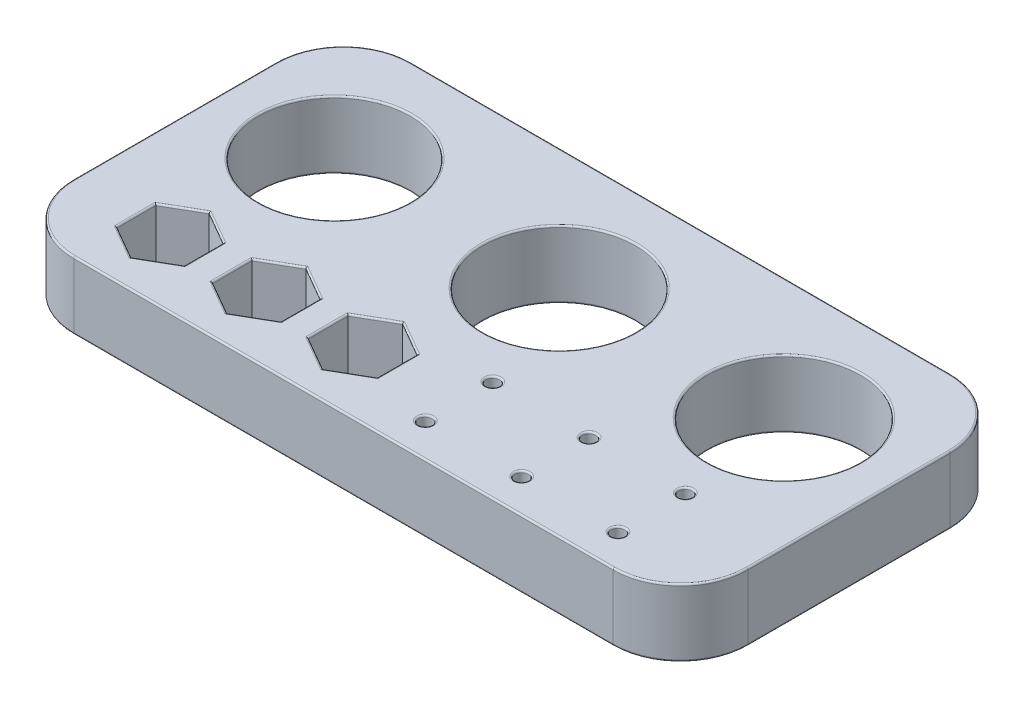
SolidWorks part; units mm, degrees
ref_plane "Front Plane" through (0, 0, 0) normal (0, 0, 1) x (1, 0, 0)
ref_plane "Top Plane" through (0, 0, 0) normal (0, 1, 0) x (1, 0, 0)
ref_plane "Right Plane" through (0, 0, 0) normal (1, 0, 0) x (0, 0, -1)
sketch "Sketch1" plane through (0, 0, 0) normal (0, 1, 0) x (1, 0, 0)
  line L0 (-63.5, -19.05) -> (-45.3571, -19.05) construction
  line L1 (-63.5, -31.75) -> (63.5, -31.75)
  line L2 (-63.5, -31.75) -> (-63.5, 31.75)
  line L3 (-63.5, 31.75) -> (63.5, 31.75)
  line L4 (63.5, -31.75) -> (63.5, 31.75)
  line L5 (-63.5, -31.75) -> (63.5, 31.75) construction
  line L6 (-63.5, 31.75) -> (63.5, -31.75) construction
  line L7 (-39.0071, -15.3838) -> (-45.3571, -11.7177)
  line L8 (-45.3571, -11.7177) -> (-51.7071, -15.3838)
  line L9 (-51.7071, -15.3838) -> (-51.7071, -22.7162)
  line L10 (-51.7071, -22.7162) -> (-45.3571, -26.3823)
  line L11 (-45.3571, -26.3823) -> (-39.0071, -22.7162)
  line L12 (-39.0071, -22.7162) -> (-39.0071, -15.3838)
  line L13 (-45.3571, -19.05) -> (-27.2143, -19.05) construction
  line L14 (-27.2143, -19.05) -> (-9.0714, -19.05) construction
  line L15 (-9.0714, -19.05) -> (9.0714, -19.05) construction
  line L16 (9.0714, -19.05) -> (27.2143, -19.05) construction
  line L17 (27.2143, -19.05) -> (45.3571, -19.05) construction
  line L18 (63.5, 8.89) -> (42.3333, 8.89) construction
  line L19 (42.3333, 8.89) -> (21.1667, 8.89) construction
  line L20 (21.1667, 8.89) -> (0, 8.89) construction
  line L21 (0, 8.89) -> (-21.1667, 8.89) construction
  line L22 (-21.1667, 8.89) -> (-42.3333, 8.89) construction
  line L23 (-42.3333, 8.89) -> (-63.5, 8.89) construction
  line L24 (-63.5, -29.21) -> (-42.3333, -29.21) construction
  line L25 (-20.7893, -22.7595) -> (-20.7893, -15.3405)
  line L26 (-20.7893, -15.3405) -> (-27.2143, -11.631)
  line L27 (-27.2143, -11.631) -> (-33.6393, -15.3405)
  line L28 (-33.6393, -15.3405) -> (-33.6393, -22.7595)
  line L29 (-33.6393, -22.7595) -> (-27.2143, -26.469)
  line L30 (-27.2143, -26.469) -> (-20.7893, -22.7595)
  line L31 (-2.5714, -22.8028) -> (-2.5714, -15.2972)
  line L32 (-2.5714, -15.2972) -> (-9.0714, -11.5444)
  line L33 (-9.0714, -11.5444) -> (-15.5714, -15.2972)
  line L34 (-15.5714, -15.2972) -> (-15.5714, -22.8028)
  line L35 (-15.5714, -22.8028) -> (-9.0714, -26.5556)
  line L36 (-9.0714, -26.5556) -> (-2.5714, -22.8028)
  line L49 (-42.3333, -29.21) -> (-21.1667, -29.21) construction
  line L50 (-21.1667, -29.21) -> (0, -29.21) construction
  line L51 (0, -29.21) -> (21.1667, -29.21) construction
  line L52 (21.1667, -29.21) -> (42.3333, -29.21) construction
  line L53 (42.3333, -29.21) -> (63.5, -29.21) construction
  line L58 (45.3571, -19.05) -> (63.5, -19.05) construction
  line L71 (0, -12.7) -> (9.0714, -12.7) construction
  line L79 (9.0714, -12.7) -> (27.2143, -12.7) construction
  line L80 (0, -19.05) -> (0, -12.7) construction
  line L81 (0, -19.05) -> (0, -25.4) construction
  line L82 (27.2143, -12.7) -> (45.3571, -12.7) construction
  line L83 (45.3571, -12.7) -> (63.5, -12.7) construction
  line L84 (0, -25.4) -> (9.0714, -25.4) construction
  line L85 (9.0714, -25.4) -> (27.2143, -25.4) construction
  line L86 (27.2143, -25.4) -> (45.3571, -25.4) construction
  line L87 (45.3571, -25.4) -> (63.5, -25.4) construction
  line L88 (9.0714, -12.7) -> (9.0714, -19.05) construction
  line L89 (9.0714, -19.05) -> (9.0714, -25.4) construction
  circle A0 centre (-42.3333, 8.89) radius 14.2875
  circle A1 centre (-45.3571, -19.05) radius 6.35 construction
  circle A2 centre (0, 8.89) radius 14.3625
  circle A3 centre (42.3333, 8.89) radius 14.4375
  circle A4 centre (-27.2143, -19.05) radius 6.425 construction
  circle A5 centre (-9.0714, -19.05) radius 6.5 construction
  circle A6 centre (9.0714, -12.7) radius 1.27
  circle A7 centre (27.2143, -12.7) radius 1.27
  circle A16 centre (45.3571, -12.7) radius 1.27
  circle A20 centre (45.3571, -25.4) radius 1.27
  circle A21 centre (27.2143, -25.4) radius 1.27
  circle A22 centre (9.0714, -25.4) radius 1.27
  point P0 (0, 0)
  point P66 (0, 0)
  dimension "D4" = 28.575
  dimension "D13" = 28.725
  dimension "D14" = 28.875
  dimension "D9" = 2.54
  dimension "D1" = 127
  dimension "D2" = 63.5
  dimension "D5" = 22.86
  dimension "D7" = 12.85
  dimension "D8" = 13
  dimension "D3" = 12.7
  dimension "D11" = 60.96
  dimension "D18" = 12.7
  dimension "D6" = 6.35
extrude "Test Plate" add sketch "Sketch1" along normal blind 12.7
hole_wizard "1/4 (0.25) Thru Hole" positions "Sketch6" profile "Sketch5" hole size "1/4" standard "ANSI Inch"
sketch "Sketch6" plane through (0, 12.7, 0) normal (0, 1, 0) x (1, 0, 0)
  point P0 (21.1667, -3.81)
  point P3 (21.1667, 21.59)
  point P6 (21.1667, 21.59)
  point P8 (21.1667, -3.81)
  point P10 (9.0714, -12.7)
  point P13 (27.2143, -12.7)
  point P16 (45.3571, -12.7)
sketch "Sketch5" plane through (21.1667, 12.7, 3.81) normal (1, 0, 0) x (0, 0, 1)
  line L0 (0, 0) -> (0, 12.7)
  line L1 (0, 12.7) -> (3.175, 12.7)
  line L2 (3.175, 12.7) -> (3.175, 0)
  line L5 (3.175, 0) -> (0, 0)
  line L11 (0, -6.35) -> (0, 107.95) construction
  dimension "Thru Hole Dia." = 6.35
  dimension "Thru Hole Depth" = 12.7
hole_wizard "#10 (0.1935) Thru Hole" positions "Sketch7" profile "Sketch8" hole size "#10" standard "ANSI Inch"
sketch "Sketch7" plane through (0, 12.7, 0) normal (0, 1, 0) x (1, 0, 0)
  point P0 (-21.1667, -3.81)
  point P3 (-21.1667, 21.59)
  point P6 (-21.1667, 21.59)
  point P8 (-21.1667, -3.81)
  point P10 (-21.1667, -3.81)
  point P12 (-21.1667, -3.81)
  point P14 (-21.1667, 21.59)
  point P16 (-41.2157, 26.4835)
  point P22 (9.0714, -25.4)
  point P25 (27.2143, -25.4)
  point P28 (45.3571, -25.4)
  point P32 (-41.2157, 26.4835)
  point P34 (-21.1667, 21.59)
  point P36 (-21.1667, -3.81)
sketch "Sketch8" plane through (-21.1667, 12.7, 3.81) normal (1, 0, 0) x (0, 0, 1)
  line L0 (0, 0) -> (0, 12.7)
  line L1 (0, 12.7) -> (2.4574, 12.7)
  line L2 (2.4574, 12.7) -> (2.4574, 0)
  line L5 (2.4574, 0) -> (0, 0)
  line L11 (0, -6.35) -> (0, 107.95) construction
  dimension "Thru Hole Dia." = 4.9149
  dimension "Thru Hole Depth" = 12.7
sketch "Sketch9" [suppressed] plane through (0, 12.7, 0) normal (0, 1, 0) x (1, 0, 0)
  circle A0 centre (-21.1667, 21.59) radius 2.6074
  circle A1 centre (21.1667, 21.59) radius 3.325
  circle A2 centre (-21.1667, 21.59) radius 2.4574 construction
  circle A3 centre (21.1667, 21.59) radius 3.175 construction
  dimension "D1" = 0.15
  dimension "D2" = 0.15
extrude "Half Max Tolerance Bolt Holes" [suppressed] cut sketch "Sketch9" against normal through all
fillet "Corner Fillet" radius 12.7 4 edges at (-63.5, 6.35, -31.75) (63.5, 6.35, -31.75) (63.5, 6.35, 31.75) (-63.5, 6.35, 31.75)
fillet "Face Smooth" radius 0.3175 70 edges at (-63.5, 0, 0) (-63.5, 12.7, 0) (63.5, 0, 0) (0, 0, 31.75) (0, 0, -31.75) (-59.7803, 0, 28.0303) (59.7803, 0, 28.0303) (59.7803, 0, -28.0303) (-59.7803, 0, -28.0303) (0, 12.7, -31.75) (63.5, 12.7, 0) (0, 12.7, 31.75) (-59.7803, 12.7, 28.0303) (0, 0, 5.4725) (59.7803, 12.7, 28.0303) (59.7803, 12.7, -28.0303) (-59.7803, 12.7, -28.0303) (0, 12.7, 5.4725) (-42.3333, 0, 5.3975) (-42.3333, 12.7, 5.3975) (42.3333, 0, 5.5475) (42.3333, 12.7, 5.5475) (-39.0071, 0, 19.05) (-42.1821, 0, 13.5507) (-48.5321, 0, 13.5507) (-51.7071, 0, 19.05) (-48.5321, 0, 24.5493) (-42.1821, 0, 24.5493) (-39.0071, 12.7, 19.05) (-42.1821, 12.7, 13.5507) (-48.5321, 12.7, 13.5507) (-51.7071, 12.7, 19.05) (-48.5321, 12.7, 24.5493) (-42.1821, 12.7, 24.5493) (-24.0018, 0, 24.6142) (-20.7893, 0, 19.05) (-24.0018, 0, 13.4858) (-30.4268, 0, 13.4858) (-33.6393, 0, 19.05) (-30.4268, 0, 24.6142) (-24.0018, 12.7, 24.6142) (-20.7893, 12.7, 19.05) (-24.0018, 12.7, 13.4858) (-30.4268, 12.7, 13.4858) (-33.6393, 12.7, 19.05) (-30.4268, 12.7, 24.6142) (-5.8214, 0, 24.6792) (-2.5714, 0, 19.05) (-5.8214, 0, 13.4208) (-12.3214, 0, 13.4208) (-15.5714, 0, 19.05) (-12.3214, 0, 24.6792) (-5.8214, 12.7, 24.6792) (-2.5714, 12.7, 19.05) (-5.8214, 12.7, 13.4208) (-12.3214, 12.7, 13.4208) (-15.5714, 12.7, 19.05) (-12.3214, 12.7, 24.6792) (9.0714, 0, 13.97) (9.0714, 12.7, 13.97) (27.2143, 0, 13.97) (27.2143, 12.7, 13.97) (45.3571, 0, 13.97) (45.3571, 12.7, 13.97) (45.3571, 0, 26.67) (45.3571, 12.7, 26.67) (27.2143, 0, 26.67) (27.2143, 12.7, 26.67) (9.0714, 0, 26.67) (9.0714, 12.7, 26.67)
sketch "Sketch10" [suppressed] plane through (0, 12.7, 0) normal (0, 1, 0) x (1, 0, 0)
  line L0 (-42.3333, 8.89) -> (-42.3333, 26.162) construction
  line L1 (0, 8.89) -> (0, 26.162) construction
  line L2 (42.3333, 8.89) -> (42.3333, 26.162) construction
  line L3 (-45.5083, 26.162) -> (-39.1583, 26.162) construction
  line L4 (-3.175, 26.162) -> (3.175, 26.162) construction
  line L5 (39.1583, 26.162) -> (45.5083, 26.162) construction
  line L7 (-42.3333, -6.985) -> (-42.3333, 10.287) construction
  line L8 (0, -6.985) -> (0, 10.287) construction
  line L9 (42.3333, -6.985) -> (42.3333, 10.287) construction
  line L10 (-45.5083, 10.287) -> (-39.1583, 10.287) construction
  line L11 (-3.175, 10.287) -> (3.175, 10.287) construction
  line L12 (45.5083, 10.287) -> (39.1583, 10.287) construction
  line L13 (-51.7071, -19.05) -> (-39.0071, -19.05) construction
  line L14 (-51.7071, -15.3838) -> (-51.7071, -22.7162) construction
  line L15 (-39.0071, -22.7162) -> (-39.0071, -15.3838) construction
  line L16 (-33.6393, -19.05) -> (-20.7893, -19.05) construction
  line L17 (-33.6393, -15.3405) -> (-33.6393, -22.7595) construction
  line L18 (-20.7893, -22.7595) -> (-20.7893, -15.3405) construction
  line L19 (-15.5714, -19.05) -> (-2.5714, -19.05) construction
  line L20 (-15.5714, -15.2972) -> (-15.5714, -22.8028) construction
  line L21 (-2.5714, -22.8028) -> (-2.5714, -15.2972) construction
  line L22 (2.6314, -19.05) -> (15.5114, -19.05) construction
  line L23 (2.6314, -15.3319) -> (2.6314, -22.7681) construction
  line L24 (15.5114, -22.7681) -> (15.5114, -15.3319) construction
  line L25 (20.7443, -19.05) -> (33.6843, -19.05) construction
  line L26 (20.7443, -15.3145) -> (20.7443, -22.7855) construction
  line L27 (33.6843, -22.7855) -> (33.6843, -15.3145) construction
  line L28 (38.8571, -19.05) -> (51.8571, -19.05) construction
  line L29 (38.8571, -15.2972) -> (38.8571, -22.8028) construction
  line L30 (51.8571, -22.8028) -> (51.8571, -15.2972) construction
  line L31 (21.1667, 21.59) -> (21.1667, 26.67) construction
  line L32 (-21.1667, 21.59) -> (-21.1667, 26.67) construction
  line L33 (-21.1667, -3.81) -> (-21.1667, 1.27) construction
  line L34 (21.1667, -3.81) -> (21.1667, 1.27) construction
  line L35 (-27.5167, 26.67) -> (-14.8167, 26.67) construction
  line L36 (-27.5167, 1.27) -> (-14.8167, 1.27) construction
  line L37 (14.8167, 1.27) -> (27.5167, 1.27) construction
  line L38 (14.8167, 26.67) -> (27.5167, 26.67) construction
  line L39 (-45.3571, -19.05) -> (-45.3571, -10.16) construction
  line L40 (-27.2143, -19.05) -> (-27.2143, -10.16) construction
  line L41 (-9.0714, -19.05) -> (-9.0714, -10.16) construction
  line L42 (9.0714, -19.05) -> (9.0714, -10.16) construction
  line L43 (27.2143, -19.05) -> (27.2143, -10.16) construction
  line L44 (45.3571, -19.05) -> (45.3571, -10.16) construction
  line L45 (-48.5321, -10.16) -> (-42.1821, -10.16) construction
  line L46 (-30.3893, -10.16) -> (-24.0393, -10.16) construction
  line L47 (-12.2464, -10.16) -> (-5.8964, -10.16) construction
  line L48 (5.8964, -10.16) -> (12.2464, -10.16) construction
  line L49 (24.0393, -10.16) -> (30.3893, -10.16) construction
  line L50 (42.1821, -10.16) -> (48.5321, -10.16) construction
  line L51 (-21.1667, 1.27) -> (-21.1667, 31.75) construction
  line L52 (63.5, 31.75) -> (-63.5, 31.75) construction
  line L53 (21.1667, 1.27) -> (21.1667, 31.75) construction
  line L54 (-26.2467, 19.05) -> (-16.0867, 19.05) construction
  line L55 (16.0867, 19.05) -> (26.2467, 19.05) construction
  line L56 (-26.2467, 15.24) -> (-16.0867, 15.24) construction
  line L57 (26.2467, 15.24) -> (16.0867, 15.24) construction
  text T0 "1" font "Impact" height 3.5
  text T1 "2" font "Impact" height 3.5
  text T2 "Start" font "Impact" height 3.5
  text T3 "0.0" font "Impact" height 3.5
  text T4 "End" font "Impact" height 3.5
  text T5 "0.5" font "Impact" height 3.5
  text T6 "#10" font "Impact" height 3.5
  text T7 "1/4-20" font "Impact" height 3.5
  text T8 "#10+" font "Impact" height 3.5
  text T9 "1/4-20+" font "Impact" height 3.5
  text T10 "1" font "Impact" height 3.5
  text T11 "2" font "Impact" height 3.5
  text T12 "3" font "Impact" height 3.5
  text T13 "4" font "Impact" height 3.5
  text T14 "5" font "Impact" height 3.5
  text T15 "6" font "Impact" height 3.5
  text T16 "3" font "Impact" height 3.5
  text T17 "4" font "Impact" height 3.5
  text T18 "5" font "Impact" height 3.5
  text T19 "6" font "Impact" height 3.5
  point P13 (-42.3333, 26.162)
  point P16 (0, 26.162)
  point P19 (42.3333, 26.162)
  point P32 (-42.3333, 10.287)
  point P35 (0, 10.287)
  point P38 (42.3333, 10.287)
  point P91 (-21.1667, 26.67)
  point P94 (-21.1667, 1.27)
  point P97 (21.1667, 1.27)
  point P100 (21.1667, 26.67)
  point P115 (-45.3571, -10.16)
  point P118 (-27.2143, -10.16)
  point P121 (-9.0714, -10.16)
  point P124 (9.0714, -10.16)
  point P127 (27.2143, -10.16)
  point P130 (45.3571, -10.16)
  point P137 (-21.1667, 19.05)
  point P140 (21.1667, 19.05)
  point P144 (-21.1667, 15.24)
  point P147 (21.1667, 15.24)
  dimension "D1" = 6.35
  dimension "D2" = 17.272
  dimension "D3" = 6.35
  dimension "D4" = 8.89
  dimension "D5" = 5.08
  dimension "D6" = 12.7
  dimension "D7" = 10.16
  dimension "D8" = 12.7
  dimension "D9" = 3.81
extrude "Labeling" [suppressed] cut sketch "Sketch10" against normal blind 2.54
equation "\"Start Tolerance\"= 0.0mm'First Hole Offset."
equation "\"End Tolerance\" = 0.3mm'Final Hole Offset. In between is Interpolated"
equation "\"Hole Diameter\" = 1.125in"
equation "\"Hex Width\"= .5in"
equation "\"D4@Sketch1\"=\"Hole Diameter\" + \"Start Tolerance\""
equation "\"D13@Sketch1\"=\"Hole Diameter\" + 0.5 * (\"End Tolerance\" - \"Start Tolerance\")"
equation "\"D14@Sketch1\"=\"Hole Diameter\" + \"End Tolerance\""
equation "\"D3@Sketch1\"=\"Hex Width\" + \"Start Tolerance\""
equation "\"D7@Sketch1\"=\"Hex Width\" + 0.5 * (\"End Tolerance\" - \"Start Tolerance\")"
equation "\"D8@Sketch1\"=\"Hex Width\" + \"End Tolerance\""
equation "\"D1@Sketch9\"=0.5 * (\"End Tolerance\" - \"Start Tolerance\")"
equation "\"D2@Sketch9\"=0.5 * (\"End Tolerance\" - \"Start Tolerance\")"
